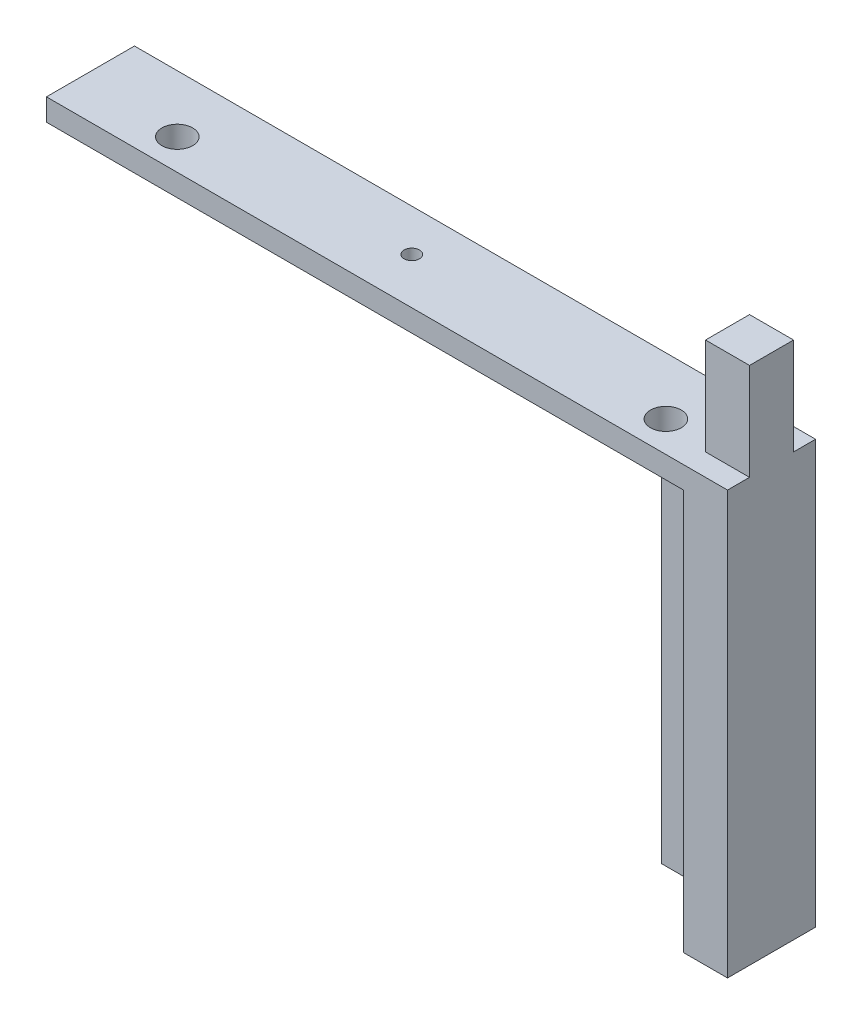
SolidWorks part; units mm, degrees
ref_plane "Front Plane" through (0, 0, 0) normal (0, 0, 1) x (1, 0, 0)
ref_plane "Top Plane" through (0, 0, 0) normal (0, 1, 0) x (1, 0, 0)
ref_plane "Right Plane" through (0, 0, 0) normal (1, 0, 0) x (0, 0, -1)
sketch "Sketch3" plane through (0, 0, 0) normal (0, 0, 1) x (1, 0, 0)
  line L0 (0, 0) -> (0, -5)
  line L1 (0, -5) -> (20, -5)
  line L2 (20, -5) -> (20, -25)
  line L3 (0, 0) -> (20, 0)
  line L4 (20, 0) -> (20, 22.02)
  line L5 (20, 22.02) -> (30, 22.02)
  line L6 (30, 22.02) -> (30, -25)
  line L7 (30, -25) -> (20, -25)
  dimension "D1" = 20
  dimension "D2" = 20
  dimension "D3" = 20
  dimension "D4" = 5
  dimension "D5" = 10
  dimension "D6" = 22.02
extrude "Boss-Extrude3" add sketch "Sketch3" along normal blind 10
sketch "Sketch4" plane through (0, 0, 0) normal (0, 0, -1) x (-1, 0, 0)
  line L5 (0, 0) -> (-30, 0)
  line L6 (0, 0) -> (0, -25)
  line L7 (0, -25) -> (-30, -25)
  line L8 (-30, 0) -> (-30, -25)
extrude "Boss-Extrude4" add sketch "Sketch4" along normal blind 5
sketch "Sketch5" plane through (0, 0, 10) normal (0, 0, 1) x (1, 0, 0)
  line L0 (0, 0) -> (0, -5)
  line L1 (0, -5) -> (20, -5)
  line L2 (20, -5) -> (20, -25)
  line L3 (20, -25) -> (30, -25)
  line L4 (30, -25) -> (30, 0)
  line L5 (30, 0) -> (0, 0)
extrude "Boss-Extrude5" add sketch "Sketch5" along normal blind 5
sketch "Sketch6" plane through (0, -25, 0) normal (0, -1, 0) x (1, 0, 0)
  line L0 (20, 15) -> (20, 0)
  line L1 (20, 0) -> (30, 0) construction
  line L2 (20, 0) -> (0, 0)
  line L3 (0, 0) -> (0, -5)
  line L4 (0, -5) -> (30, -5)
  line L5 (30, -5) -> (30, 15)
  line L6 (30, 15) -> (20, 15)
extrude "Boss-Extrude6" add sketch "Sketch6" along normal up to surface (71 mm away)
sketch "Sketch7" plane through (0, 0, 0) normal (-1, 0, 0) x (0, 0, 1)
  line L0 (-5, -96) -> (-5, 0) construction
  line L1 (15, 0) -> (-5, 0)
  line L2 (15, 0) -> (15, -5)
  line L3 (15, -5) -> (0, -5)
  line L4 (-5, 0) -> (-5, -5)
  line L6 (-5, -9.319) -> (0, -9.319)
  line L7 (-5, -9.319) -> (-5, 0)
  line L8 (-5, 0) -> (0, 0)
  line L9 (0, -9.319) -> (0, -5)
  line M1 (15, 0) -> (-5, 0)
  line M2 (-5, 0) -> (-5, -96)
  line M4 (0, -96) -> (0, -5)
  line M5 (0, -5) -> (15, -5)
  line M6 (15, -5) -> (15, 0)
extrude "Boss-Extrude7" add sketch "Sketch7" along normal blind 124.7205 contours L6 L1 M2 M4 M5 M6 M1
sketch "Sketch9" plane through (0, 0, -5) normal (0, 0, -1) x (-1, 0, 0)
  circle A0 centre (-13, -15) radius 3.25
extrude "Cut-Extrude1" cut sketch "Sketch9" against normal blind 15
sketch "Sketch13" plane through (0, 0, 0) normal (0, 1, 0) x (1, 0, 0)
  line L2 (-124.7205, -15) -> (-124.7205, 5) construction
  line L3 (-124.7205, 5) -> (30, 5) construction
  circle A0 centre (-52.2205, -4.5009) radius 1.75
  dimension "D1" = 3.5
  dimension "D2" = 72.5
  dimension "D3" = 9.5009
extrude "Cut-Extrude2" cut sketch "Sketch13" against normal blind 10 and the other way blind 8
sketch "Sketch14" plane through (0, 0, 0) normal (0, 1, 0) x (1, 0, 0)
  circle A0 centre (-102, -8) radius 3.5
extrude "Cut-Extrude3" cut sketch "Sketch14" against normal blind 12 and the other way blind 8
sketch "Sketch15" plane through (0, 0, 0) normal (0, 1, 0) x (1, 0, 0)
  circle A0 centre (9, -8) radius 3.5
extrude "Cut-Extrude4" cut sketch "Sketch15" against normal blind 17 and the other way blind 4
